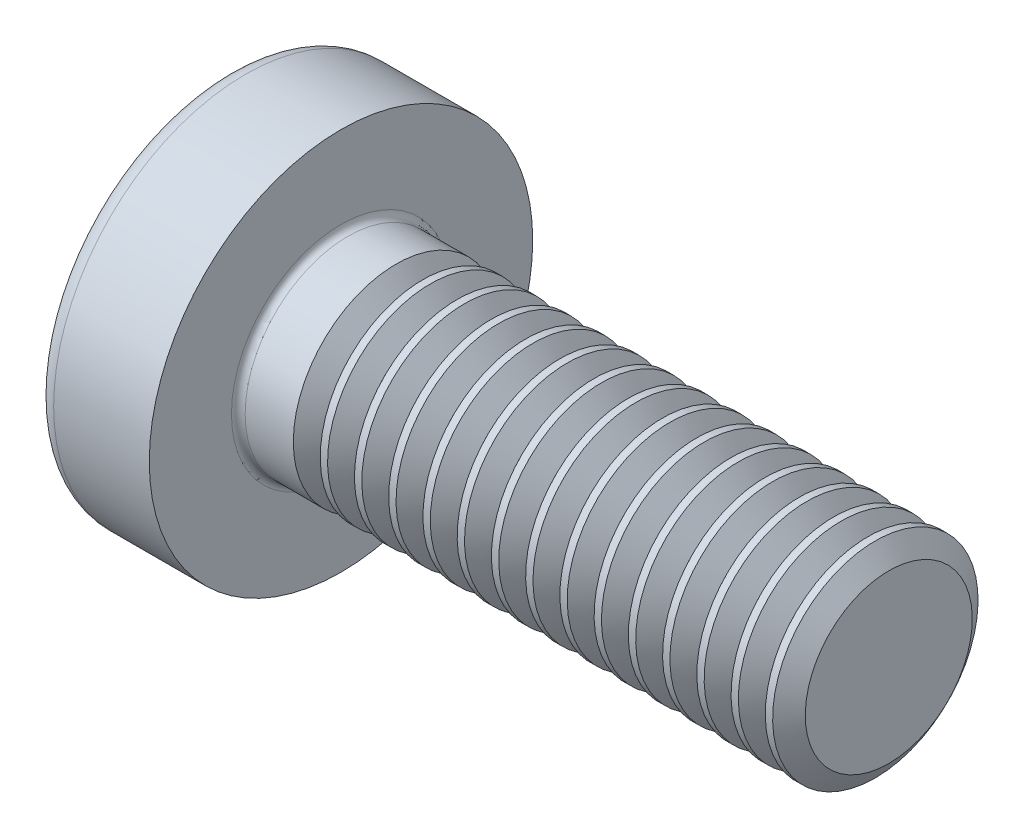
SolidWorks part; units mm, degrees
ref_plane "Plane1" through (0, 0, 0) normal (0, 0, 1) x (1, 0, 0)
ref_plane "Plane2" through (0, 0, 0) normal (0, 1, 0) x (1, 0, 0)
ref_plane "Plane3" through (0, 0, 0) normal (1, 0, 0) x (0, 0, -1)
sketch "BodySke" plane through (0, 0, 0) normal (0, 0, 1) x (1, 0, 0)
  line L0 (2.4, 1.5) -> (2.4, 2.8)
  line L1 (2.65, 6.35) -> (2.65, -3.175) construction
  line L2 (-25.4, 0) -> (127, 0) construction
  line L3 (10.4, 0) -> (0, 0)
  line L4 (2.4, 1.5) -> (10.4, 1.5)
  line L5 (10.4, 1.5) -> (10.4, 0)
  line L6 (1.0035, 2.8) -> (2.4, 2.8)
  line L8 (2.4, 6.35) -> (2.4, -3.175) construction
  arc A0 (0.7754, 2.6744) -> (0, 0) centre (5, 0) ccw
  arc A2 (0.7754, 2.6744) -> (1.0035, 2.8) centre (1.0035, 2.53) cw
revolve "Base-Revolve" add sketch "BodySke"
cosmetic thread "ThreadCosmetic" [suppressed]
fillet "Fillet1" radius 0.1 1 edges at (2.4, 0, 1.5)
sketch "Sketch3" plane through (0, 0, 0) normal (1, 0, 0) x (0, 0, -1)
  line L0 (0.37, -1.4) -> (-0.37, -1.4)
  line L1 (0.37, -1.4) -> (0.37, 1.4)
  line L2 (-0.37, 1.4) -> (0.37, 1.4)
  line L3 (-0.37, 1.4) -> (-0.37, -1.4)
ref_plane "Plane4" through (1.75, 0, 0) normal (1, 0, 0) x (0, 0, -1)
sketch "Sketch4" plane through (1.75, 0, 0) normal (1, 0, 0) x (0, 0, -1)
  line L0 (0.37, -0.5275) -> (-0.37, -0.5275)
  line L1 (0.37, -0.5275) -> (0.37, 0.5275)
  line L2 (-0.37, 0.5275) -> (0.37, 0.5275)
  line L3 (-0.37, 0.5275) -> (-0.37, -0.5275)
loft "Recess" cut profiles "Sketch3", "Sketch4"
pattern_circular "RecPat" count 2 every 90 about axis through (0, 0, 0) along (1, 0, 0) of "Recess"
sketch "RecCorSke" plane through (0, 0, 0) normal (0, 0, 1) x (1, 0, 0)
  line L0 (-3.175, 0) -> (15.875, 0) construction
  line L1 (-25.4, 0) -> (127, 0) construction
  line L2 (0, 0) -> (0, 0.6784)
  line L3 (0, 0.6784) -> (1.75, 0.556)
  line L4 (1.75, 0.556) -> (1.9307, 0)
  line L5 (1.9307, 0) -> (0, 0)
revolve "RecessCore" cut sketch "RecCorSke" angle 360 about L0
sketch "ThdSchSke" plane through (0, 0, 0) normal (0, 0, 1) x (1, 0, 0)
  line L0 (3.4, -1.2195) -> (3.2036, -1.5)
  line L1 (3.4, -1.2195) -> (3.5964, -1.5)
  line L2 (3.5964, -1.5) -> (3.5964, -1.875)
  line L3 (-3.175, 0) -> (5.1513, 0) construction
  line L5 (3.5964, -1.875) -> (3.2036, -1.875)
  line L6 (3.2036, -1.875) -> (3.2036, -1.5)
revolve "ThreadSchematic" cut sketch "ThdSchSke" angle 360 about L3
pattern_linear "ThdSchPat" count 15 spacing 0.5 along (1, 0, 0) of "ThreadSchematic"
equation "\"D1@Sketch3\" = \"Cross_dia@Sketch3\" / 2"
equation "\"D2@Sketch3\" = \"Cross_width@Sketch3\" / 2"
equation "\"Depth@RecCorSke\" = \"Cross_depth@Plane4\""
equation "\"D1@Sketch4\" = \"Cross_width@Sketch3\""
equation "\"D2@Sketch4\" = \"Cross_dia@Sketch3\" - 2.0 * \"Cross_depth@Plane4\" * tan(26.5  * 0.017453292)"
equation "\"D3@Sketch4\" = \"D1@Sketch4\" / 2"
equation "\"D4@Sketch4\" = \"D2@Sketch4\" / 2"
equation "\"Thread_length@ThreadCosmetic\" = ((sgn( (\"Length@BodySke\" - \"Advance@BodySke\" * 2.0 ) - \"Thread_nom@BodySke\" )-1)*( (\"Length@BodySke\" - \"Advance@BodySke\" * 2.0 ) - \"Thread_nom@BodySke\" ))/-2+ \"Thread_nom@BodySke\""
equation "\"Thread_minor@ThdSchSke\" = \"Thread_minor@ThreadCosmetic\""
equation "\"Diameter@ThdSchSke\" = \"Diameter@BodySke\""
equation "\"Overcut@ThdSchSke\" = \"Diameter@BodySke\" * 1.25"
equation "\"Start@ThdSchSke\" = \"Head_ht@BodySke\" + \"Length@BodySke\" - \"Thread_length@ThreadCosmetic\"  '---Non-countersunk---"
equation "\"Num_threads@ThdSchPat\" = int( \"Thread_length@ThreadCosmetic\" / \"Advance@BodySke\" + 0.999 )  + 1"
equation "\"Advance@ThdSchPat\" = \"Thread_length@ThreadCosmetic\" /  (\"Num_threads@ThdSchPat\" - 1) 'relax it"
